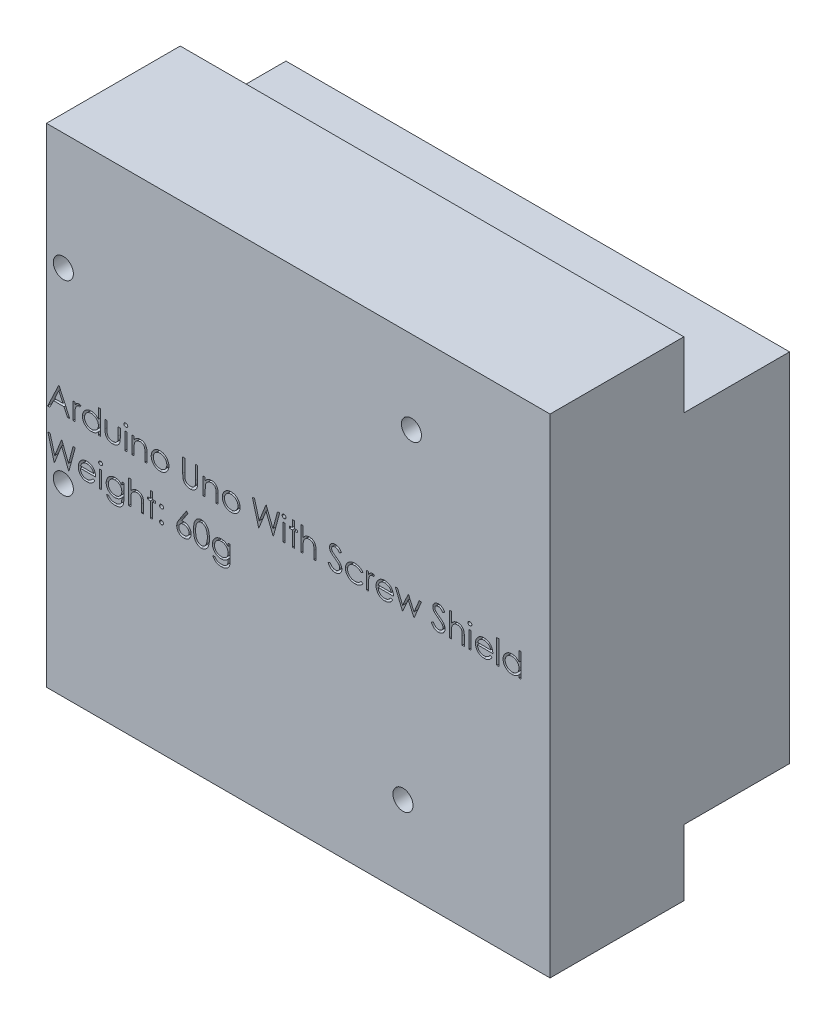
SolidWorks part; units mm, degrees
ref_plane "Front Plane" through (0, 0, 0) normal (0, 0, 1) x (1, 0, 0)
ref_plane "Top Plane" through (0, 0, 0) normal (0, 1, 0) x (1, 0, 0)
ref_plane "Right Plane" through (0, 0, 0) normal (1, 0, 0) x (0, 0, -1)
sketch "Sketch1" plane through (0, 0, 0) normal (0, 0, 1) x (1, 0, 0)
  line L0 (-37.6375, 36.5) -> (37.6375, 36.5)
  line L1 (-37.6375, 36.5) -> (-37.6375, -36.5)
  line L2 (-37.6375, -36.5) -> (37.6375, -36.5)
  line L3 (37.6375, 36.5) -> (37.6375, -36.5)
  line L4 (0, -36.5) -> (0, 36.5) construction
  line L5 (-37.6375, 0) -> (37.6375, 0) construction
  line L6 (-35.1125, 26.65) -> (-35.1125, -26.65) construction
  line L7 (-37.6425, -26.65) -> (37.6375, -26.65)
  line L8 (-37.6425, -26.65) -> (-37.6425, 26.65)
  line L9 (-37.6425, 26.65) -> (37.6375, 26.65)
  line L10 (37.6375, -26.65) -> (37.6375, 26.65)
  line L11 (-0.0025, 26.65) -> (-0.0025, -26.65) construction
  line L12 (-37.6425, 0) -> (37.6375, 0) construction
  circle A0 centre (16.9175, 24.111) radius 1.5
  circle A1 centre (15.6525, -24.411) radius 1.5
  circle A2 centre (-35.1125, 19.033) radius 1.5
  circle A3 centre (-35.1125, -8.876) radius 1.5
  point P22 (0, 0)
  point P27 (-0.0025, 0)
  dimension "D6" = 3
  dimension "D7" = 3
  dimension "D13" = 3
  dimension "D14" = 3
  dimension "D1" = 73
  dimension "D2" = 75.275
  dimension "D3" = 75.28
  dimension "D4" = 53.3
  dimension "D5" = 0
  dimension "D8" = 20.72
  dimension "D9" = 2.539
  dimension "D10" = 21.985
  dimension "D11" = 48.522
  dimension "D12" = 52.03
  dimension "D15" = 27.909
  dimension "D16" = 7.617
extrude "Boss-Extrude1" add sketch "Sketch1" along normal blind 15.8 contours L9 L1 L7 L3 A3 A2 A1 A0
sketch "Sketch3" plane through (0, 0, 15.8) normal (0, 0, 1) x (1, 0, 0)
  line L0 (-37.6375, 36.5) -> (37.6375, 36.5)
  line L1 (-37.6375, 36.5) -> (-37.6375, -36.5)
  line L2 (-37.6375, -36.5) -> (37.6375, -36.5)
  line L3 (37.6375, 36.5) -> (37.6375, -36.5)
  line L4 (0, -36.5) -> (0, 36.5) construction
  line L5 (-37.6375, 0) -> (37.6375, 0) construction
  line L6 (-35.1125, 26.65) -> (-35.1125, -26.65) construction
  line L7 (-37.6425, -26.65) -> (37.6375, -26.65)
  line L8 (-37.6425, -26.65) -> (-37.6425, 26.65)
  line L9 (-37.6425, 26.65) -> (37.6375, 26.65)
  line L10 (37.6375, -26.65) -> (37.6375, 26.65)
  line L11 (-0.0025, 26.65) -> (-0.0025, -26.65) construction
  line L12 (-37.6425, 0) -> (37.6375, 0) construction
  line L13 (37.6375, 26.65) -> (37.6375, -26.65) construction
  line L14 (-37.6375, -26.65) -> (37.6375, -26.65) construction
  circle A0 centre (16.9175, 24.111) radius 1.5
  circle A1 centre (15.6525, -24.411) radius 1.5
  circle A2 centre (-35.1125, 19.033) radius 1.5
  circle A3 centre (-35.1125, -8.876) radius 1.5
  point P22 (0, 0)
  point P27 (-0.0025, 0)
  circle M3 centre (-35.1125, -8.876) radius 1.5
  circle M4 centre (-35.1125, 19.033) radius 1.5
  circle M5 centre (15.6525, -24.411) radius 1.5
  circle M6 centre (16.9175, 24.111) radius 1.5
  line M7 (37.6375, 26.65) -> (-37.6375, 26.65)
  line M8 (-37.6375, 26.65) -> (-37.6375, -26.65)
  line M9 (-37.6375, -26.65) -> (37.6375, -26.65)
  line M10 (37.6375, -26.65) -> (37.6375, 26.65)
  dimension "D6" = 3
  dimension "D7" = 3
  dimension "D13" = 3
  dimension "D14" = 3
  dimension "D1" = 73
  dimension "D2" = 75.275
  dimension "D3" = 75.28
  dimension "D4" = 53.3
  dimension "D5" = 0
  dimension "D8" = 20.72
  dimension "D9" = 2.539
  dimension "D10" = 21.985
  dimension "D11" = 48.522
  dimension "D12" = 52.03
  dimension "D15" = 27.909
  dimension "D16" = 7.617
  dimension "D17" = 0
  dimension "D18" = 0
extrude "Boss-Extrude4" add sketch "Sketch3" along normal blind 20 contours L3 L0 L1 M7 | M10 M7 M8 M9 M4 M6 M5 M3 | L3 L1 L2 M9
sketch "Sketch4" plane through (0, 0, 35.8) normal (0, 0, 1) x (1, 0, 0)
  line L0 (-37.6375, 0) -> (37.6375, 0) construction
  line L1 (-37.6375, 36.5) -> (-37.6375, -36.5) construction
  line L2 (37.6375, 36.5) -> (37.6375, -36.5) construction
  text T0 "Arduino Uno With Screw Shield\r\nWeight: 60g"
  dimension "D1" = 37.6375
  dimension "D2" = 37.6375
extrude "Cut-Extrude1" cut sketch "Sketch4" against normal blind 2
